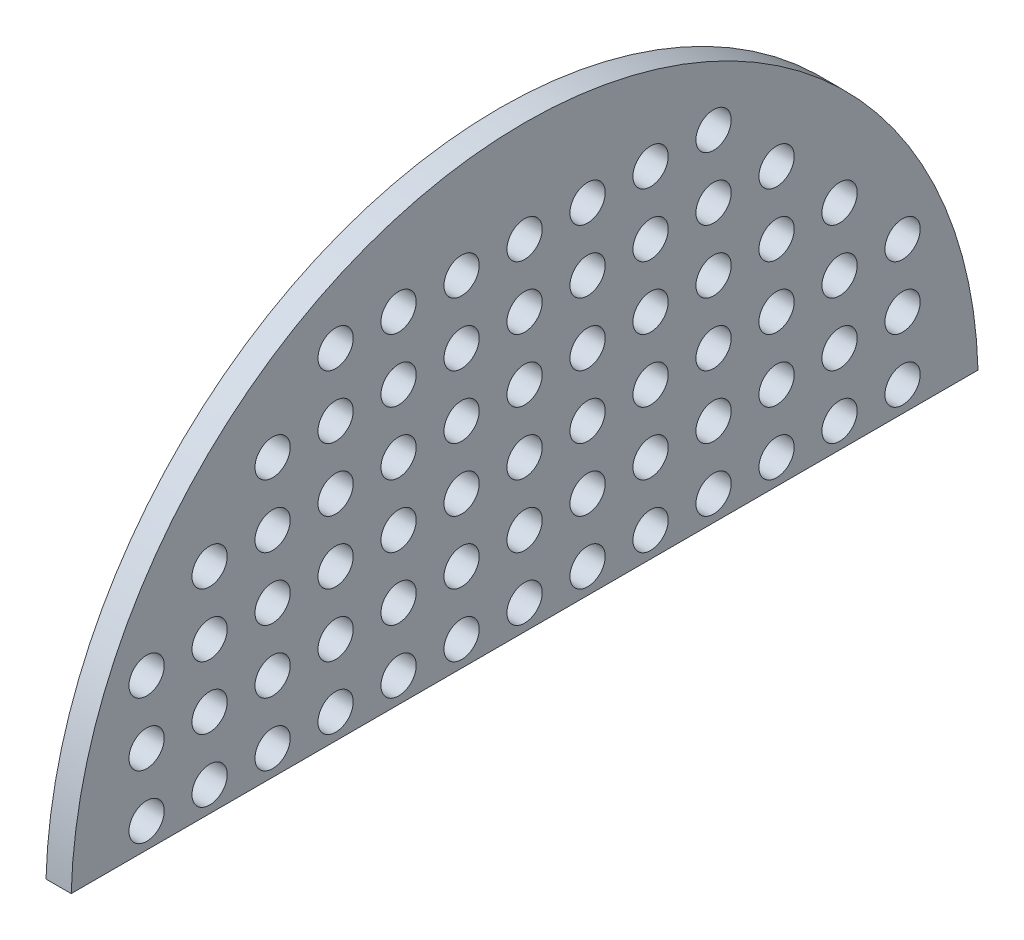
SolidWorks part; units mm, degrees
ref_plane "Front Plane" through (0, 0, 0) normal (0, 0, 1) x (1, 0, 0)
ref_plane "Top Plane" through (0, 0, 0) normal (0, 1, 0) x (1, 0, 0)
ref_plane "Right Plane" through (0, 0, 0) normal (1, 0, 0) x (0, 0, -1)
sketch "Sketch1" plane through (0, 0, 0) normal (1, 0, 0) x (0, 0, -1)
  line L0 (1800, 0) -> (-1800, 0)
  line L1 (0, 0) -> (0, 1800) construction
  arc A0 (1800, 0) -> (-1800, 0) centre (0, 0) ccw
  circle A1 centre (0, 150) radius 70
  circle A2 centre (250, 150) radius 70
  circle A3 centre (500, 150) radius 70
  circle A4 centre (750, 150) radius 70
  circle A5 centre (1000, 150) radius 70
  circle A6 centre (1250, 150) radius 70
  circle A7 centre (1500, 150) radius 70
  circle A8 centre (250, 400) radius 70
  circle A9 centre (500, 400) radius 70
  circle A10 centre (750, 400) radius 70
  circle A11 centre (1000, 400) radius 70
  circle A12 centre (1250, 400) radius 70
  circle A13 centre (1500, 400) radius 70
  circle A14 centre (250, 650) radius 70
  circle A15 centre (500, 650) radius 70
  circle A16 centre (750, 650) radius 70
  circle A17 centre (1000, 650) radius 70
  circle A18 centre (1250, 650) radius 70
  circle A19 centre (1500, 650) radius 70
  circle A20 centre (250, 900) radius 70
  circle A21 centre (500, 900) radius 70
  circle A22 centre (750, 900) radius 70
  circle A23 centre (1000, 900) radius 70
  circle A24 centre (1250, 900) radius 70
  circle A26 centre (250, 1150) radius 70
  circle A27 centre (500, 1150) radius 70
  circle A28 centre (750, 1150) radius 70
  circle A29 centre (1000, 1150) radius 70
  circle A32 centre (250, 1400) radius 70
  circle A33 centre (500, 1400) radius 70
  circle A34 centre (750, 1400) radius 70
  circle A38 centre (0, 400) radius 70
  circle A39 centre (0, 650) radius 70
  circle A40 centre (0, 900) radius 70
  circle A41 centre (0, 1150) radius 70
  circle A42 centre (0, 1400) radius 70
  circle A43 centre (1500, 1150) radius 70 [skipped]
  circle A44 centre (1250, 1400) radius 70 [skipped]
  circle A45 centre (1500, 1400) radius 70 [skipped]
  arc A46 (1517.7374, 967.7155) -> (1568.096, 883.7845) centre (1500, 900) ccw [skipped]
  circle A47 centre (1250, 1150) radius 70 [skipped]
  circle A48 centre (1000, 1400) radius 70 [skipped]
  circle A49 centre (-750, 1400) radius 70
  circle A50 centre (-500, 1400) radius 70
  circle A51 centre (-250, 1400) radius 70
  circle A52 centre (-1000, 1150) radius 70
  circle A53 centre (-750, 1150) radius 70
  circle A54 centre (-500, 1150) radius 70
  circle A55 centre (-250, 1150) radius 70
  circle A56 centre (-1250, 900) radius 70
  circle A57 centre (-1000, 900) radius 70
  circle A58 centre (-750, 900) radius 70
  circle A59 centre (-500, 900) radius 70
  circle A60 centre (-250, 900) radius 70
  circle A61 centre (-1500, 650) radius 70
  circle A62 centre (-1250, 650) radius 70
  circle A63 centre (-1000, 650) radius 70
  circle A64 centre (-750, 650) radius 70
  circle A65 centre (-500, 650) radius 70
  circle A66 centre (-250, 650) radius 70
  circle A67 centre (-1500, 400) radius 70
  circle A68 centre (-1250, 400) radius 70
  circle A69 centre (-1000, 400) radius 70
  circle A70 centre (-750, 400) radius 70
  circle A71 centre (-500, 400) radius 70
  circle A72 centre (-250, 400) radius 70
  circle A73 centre (-1500, 150) radius 70
  circle A74 centre (-1250, 150) radius 70
  circle A75 centre (-1000, 150) radius 70
  circle A76 centre (-750, 150) radius 70
  circle A77 centre (-500, 150) radius 70
  circle A78 centre (-250, 150) radius 70
  dimension "D1" = 3600
  dimension "D2" = 7
  dimension "D3" = 6
extrude "Boss-Extrude1" add sketch "Sketch1" along normal blind 100
sketch "Sketch2" plane through (100, 0, 0) normal (1, 0, 0) x (0, 0, -1)
  line L1 (1827.6913, -50) -> (-1827.6913, -50)
  line L2 (1827.6913, -50) -> (1827.6913, 50)
  line L3 (1827.6913, 50) -> (-1827.6913, 50)
  line L4 (-1827.6913, -50) -> (-1827.6913, 50)
  line L5 (1827.6913, -50) -> (-1827.6913, 50) construction
  line L6 (1827.6913, 50) -> (-1827.6913, -50) construction
  point P0 (0, 0)
  dimension "D1" = 100
extrude "Cut-Extrude1" cut sketch "Sketch2" against normal through all
